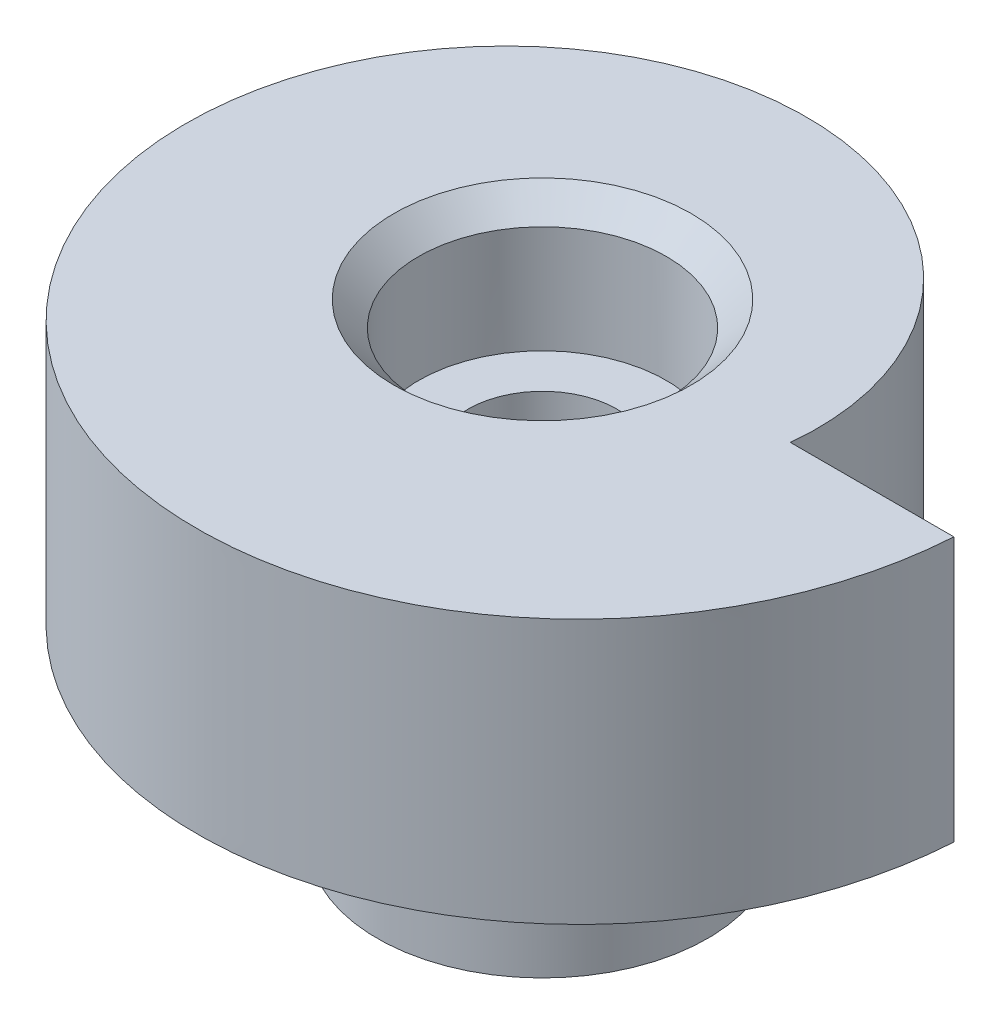
SolidWorks part; units mm, degrees
ref_plane "Спереди" through (0, 0, 0) normal (0, 0, 1) x (1, 0, 0)
ref_plane "Сверху" through (0, 0, 0) normal (0, 1, 0) x (1, 0, 0)
ref_plane "Справа" through (0, 0, 0) normal (1, 0, 0) x (0, 0, -1)
sketch "Эскиз1" plane through (0, 0, 0) normal (0, 1, 0) x (1, 0, 0)
  line L0 (6, 0) -> (9.9584, 0)
  circle A0 centre (0, 0) radius 1.8
  circle A1 centre (0, 0) radius 10 construction
  spline S0 degree 4 poles (4.5338, -3.2941) (4.6118, -3.2087) (4.7629, -3.0339) (4.9749, -2.7593) (5.2268, -2.3712) (5.4455, -1.9659) (5.6304, -1.5456) (5.7622, -1.1684) (5.8461, -0.8663) (5.897, -0.6451) (5.9251, -0.5076) (5.9456, -0.3956) (5.9645, -0.278) (5.9816, -0.1562) (5.9952, -0.0471) (6.0041, 0.0376) (6.0151, 0.1634) (6.0248, 0.3041) (6.0305, 0.4348) (6.0333, 0.5867) (6.0327, 0.7383) (6.0272, 0.9176) (6.0106, 1.1723) (5.9771, 1.4768) (5.9182, 1.8295) (5.8244, 2.2272) (5.7047, 2.6179) (5.5596, 2.9999) (5.39, 3.3716) (5.1968, 3.7317) (4.9809, 4.0786) (4.6839, 4.4941) (4.2864, 4.9613) (3.7677, 5.4555) (3.1095, 5.9425) (2.3968, 6.3453) (1.6406, 6.6588) (0.6553, 6.9349) (-0.3643, 7.0528) (-1.3896, 7.0109) (-2.5942, 6.7743) (-3.7526, 6.3574) (-4.994, 5.6257) (-6.1956, 4.5004) (-7.1278, 3.1439) (-7.877, 1.3204) (-8.1801, -1.0599) (-7.6994, -3.4354) (-6.5124, -5.522) (-5.0757, -6.9901) (-3.7244, -7.925) (-2.2223, -8.5902) (-0.6233, -8.9663) (1.0173, -9.0443) (2.6448, -8.8257) (4.2072, -8.321) (5.4753, -7.6461) (6.4646, -6.9177) (7.2125, -6.2209) (7.7606, -5.6142) (8.2549, -4.9629) (8.692, -4.2719) (9.022, -3.6371) (9.2659, -3.0749) (9.4426, -2.5959) (9.5679, -2.2071) (9.6768, -1.8135) (9.7693, -1.4155) (9.8356, -1.0648) (9.8784, -0.7858) (9.9043, -0.5865) (9.9189, -0.4593) (9.9298, -0.3538) (9.9424, -0.2173) (9.9544, -0.0662) (9.9618, 0.0473) (9.9703, 0.2235) (9.976, 0.3934) (9.9793, 0.5916) (9.9778, 0.8231) (9.9693, 1.1004) (9.9495, 1.4132) (9.9199, 1.7266) (9.8806, 2.0383) (9.8315, 2.3489) (9.7728, 2.6578) (9.6874, 3.0414) (9.566, 3.4972) (9.3971, 4.021) (9.2249, 4.4603) (9.0982, 4.748) (9.032, 4.8906) knots 0 0 0 0 0 0.007833 0.015666 0.023499 0.031332 0.039039 0.046747 0.050601 0.052528 0.054455 0.056382 0.058309 0.060235 0.062162 0.063893 0.065623 0.069084 0.070815 0.072545 0.076006 0.079467 0.082928 0.08985 0.096772 0.103694 0.110616 0.117538 0.12446 0.131381 0.138303 0.145225 0.159069 0.172913 0.186757 0.200601 0.214445 0.228288 0.255976 0.26982 0.283664 0.311351 0.339039 0.366727 0.394414 0.422102 0.47174 0.527115 0.554803 0.58249 0.610178 0.637866 0.665553 0.693241 0.720928 0.748616 0.776304 0.790148 0.803991 0.817835 0.831679 0.845523 0.859367 0.866289 0.873211 0.880133 0.887054 0.893976 0.900898 0.904359 0.90609 0.90782 0.909551 0.911281 0.914742 0.917406 0.920071 0.922735 0.925399 0.930728 0.936057 0.941385 0.946714 0.952042 0.957371 0.9627 0.968028 0.978686 0.989343 1 1 1 1 1 construction
  spline S1 degree 4 poles (6, 0) (6.0023, 0.0216) (6.0065, 0.065) (6.0151, 0.1634) (6.0248, 0.3041) (6.0305, 0.4348) (6.0333, 0.5867) (6.0327, 0.7383) (6.0272, 0.9176) (6.0106, 1.1723) (5.9771, 1.4768) (5.9182, 1.8295) (5.8244, 2.2272) (5.7047, 2.6179) (5.5596, 2.9999) (5.39, 3.3716) (5.1968, 3.7317) (4.9809, 4.0786) (4.6839, 4.4941) (4.2864, 4.9613) (3.7677, 5.4555) (3.1095, 5.9425) (2.3968, 6.3453) (1.6406, 6.6588) (0.6553, 6.9349) (-0.3643, 7.0528) (-1.3896, 7.0109) (-2.5942, 6.7743) (-3.7526, 6.3574) (-4.994, 5.6257) (-6.1956, 4.5004) (-7.1278, 3.1439) (-7.877, 1.3204) (-8.1801, -1.0599) (-7.6994, -3.4354) (-6.5124, -5.522) (-5.0757, -6.9901) (-3.7244, -7.925) (-2.2223, -8.5902) (-0.6233, -8.9663) (1.0173, -9.0443) (2.6448, -8.8257) (4.2072, -8.321) (5.4753, -7.6461) (6.4646, -6.9177) (7.2125, -6.2209) (7.7606, -5.6142) (8.2549, -4.9629) (8.692, -4.2719) (9.022, -3.6371) (9.2659, -3.0749) (9.4426, -2.5959) (9.5679, -2.2071) (9.6768, -1.8135) (9.7693, -1.4155) (9.8356, -1.0648) (9.8784, -0.7858) (9.9043, -0.5865) (9.9189, -0.4593) (9.9298, -0.3538) (9.9424, -0.2173) (9.951, -0.1082) (9.9557, -0.0434) (9.9584, 0) knots 0.062162 0.062162 0.062162 0.062162 0.062162 0.063893 0.065623 0.069084 0.070815 0.072545 0.076006 0.079467 0.082928 0.08985 0.096772 0.103694 0.110616 0.117538 0.12446 0.131381 0.138303 0.145225 0.159069 0.172913 0.186757 0.200601 0.214445 0.228288 0.255976 0.26982 0.283664 0.311351 0.339039 0.366727 0.394414 0.422102 0.47174 0.527115 0.554803 0.58249 0.610178 0.637866 0.665553 0.693241 0.720928 0.748616 0.776304 0.790148 0.803991 0.817835 0.831679 0.845523 0.859367 0.866289 0.873211 0.880133 0.887054 0.893976 0.900898 0.904359 0.90609 0.90782 0.909551 0.911281 0.914742 0.914742 0.914742 0.914742 0.914742
  point P4 (6.5, 0)
  point P5 (10, 0)
  dimension "D1" = 3.6
  dimension "D2" = 20
  dimension "D3" = 3.5
extrude "Бобышка-Вытянуть1" add sketch "Эскиз1" along normal blind 6.4
sketch "Эскиз7" plane through (0, 6.4, 0) normal (0, 1, 0) x (1, 0, 0)
  circle A0 centre (0, 0) radius 3
  dimension "D1" = 6
extrude "Вырез-Вытянуть1" cut sketch "Эскиз7" against normal blind 3.2
chamfer "Фаска1" distance 0.6 angle 45 1 edges at (0, 6.4, 3)
sketch "Эскиз8" plane through (0, 0, 0) normal (0, -1, 0) x (1, 0, 0)
  circle A0 centre (0, 0) radius 1.8
  circle A1 centre (0, 0) radius 4
  dimension "D1" = 8
extrude "Бобышка-Вытянуть2" add sketch "Эскиз8" along normal blind 5
sketch "Эскиз9" plane through (0, 0, 0) normal (0, -1, 0) x (1, 0, 0)
  circle A0 centre (0, 0) radius 4
  circle A1 centre (0, 0) radius 5.65
  dimension "D1" = 11.3
extrude "Вырез-Вытянуть2" cut sketch "Эскиз9" against normal blind 2
